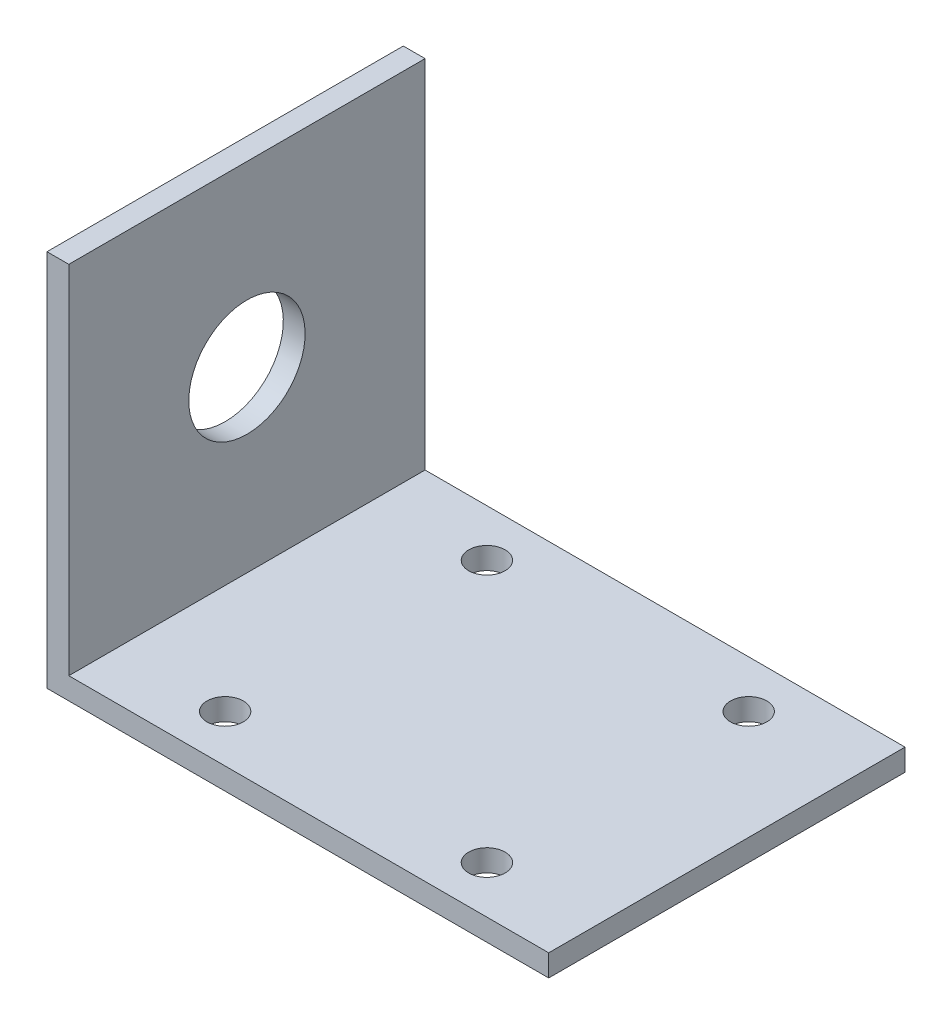
SolidWorks part; units mm, degrees
ref_plane "前视基准面" through (0, 0, 0) normal (0, 0, 1) x (1, 0, 0)
ref_plane "上视基准面" through (0, 0, 0) normal (0, 1, 0) x (1, 0, 0)
ref_plane "右视基准面" through (0, 0, 0) normal (1, 0, 0) x (0, 0, -1)
sketch "草图1" plane through (0, 0, 0) normal (0, 0, 1) x (1, 0, 0)
  line L0 (-22.5644, 30.232) -> (-22.5644, -21.768)
  line L1 (-22.5644, -21.768) -> (46.4356, -21.768)
  line L2 (46.4356, -21.768) -> (46.4356, -18.768)
  line L3 (46.4356, -18.768) -> (-19.5644, -18.768)
  line L4 (-19.5644, -18.768) -> (-19.5644, 30.232)
  line L5 (-19.5644, 30.232) -> (-22.5644, 30.232)
  dimension "D1" = 69
  dimension "D2" = 52
  dimension "D3" = 3
  dimension "D4" = 3
extrude "凸台-拉伸1" add sketch "草图1" along normal blind 49
sketch "草图2" plane through (0, -18.768, 0) normal (0, 1, 0) x (1, 0, 0)
  line L0 (-28.9678, -24.5) -> (56.4255, -24.5) construction
  line L1 (-4.5644, -6.5) -> (31.4356, -6.5) construction
  line L2 (-4.5644, -6.5) -> (-4.5644, -42.5) construction
  line L3 (-4.5644, -42.5) -> (31.4356, -42.5) construction
  line L4 (31.4356, -6.5) -> (31.4356, -42.5) construction
  line L5 (13.4356, 7.8214) -> (13.4356, -57.0775) construction
  line L7 (46.4356, -49) -> (-19.5644, -49) construction
  line L8 (46.4356, 0) -> (-19.5644, 0) construction
  line L9 (-19.5644, -49) -> (-19.5644, 0) construction
  line L10 (46.4356, -49) -> (46.4356, 0) construction
  circle A0 centre (-4.5644, -6.5) radius 2.5
  circle A1 centre (31.4356, -6.5) radius 2.5
  circle A2 centre (-4.5644, -42.5) radius 2.5
  circle A3 centre (31.4356, -42.5) radius 2.5
  dimension "D3" = 5
  dimension "D1" = 36
  dimension "D2" = 36
extrude "切除-拉伸1" cut sketch "草图2" against normal blind 49
sketch "草图3" plane through (-22.5644, 0, 0) normal (-1, 0, 0) x (0, 0, 1)
  line L0 (-5.0673, 5.732) -> (58.2271, 5.732) construction
  line L1 (24.5, 32.305) -> (24.5, -24.3963) construction
  line L2 (0, 30.232) -> (0, -21.768) construction
  line L3 (49, 30.232) -> (49, -21.768) construction
  line L6 (49, -18.768) -> (0, -18.768) construction
  line L7 (49, 30.232) -> (0, 30.232) construction
  circle A0 centre (24.5, 5.732) radius 8
  dimension "D1" = 16
extrude "切除-拉伸2" cut sketch "草图3" against normal blind 49
